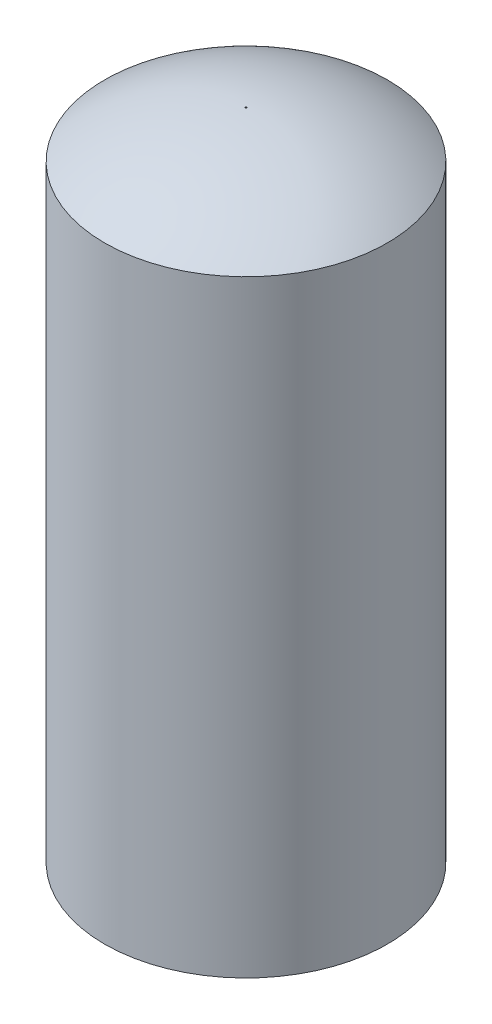
SolidWorks part; units mm, degrees
ref_plane "Спереди" through (0, 0, 0) normal (0, 0, 1) x (1, 0, 0)
ref_plane "Сверху" through (0, 0, 0) normal (0, 1, 0) x (1, 0, 0)
ref_plane "Справа" through (0, 0, 0) normal (1, 0, 0) x (0, 0, -1)
other "Центр тяжести" [suppressed]
sketch "Эскиз1" plane through (0, 0, 0) normal (1, 0, 0) x (0, 0, -1)
  line L0 (0, -42.7351) -> (0, 1057.9575) construction
  line L1 (200, 65.4384) -> (200, 934.5616)
  line L2 (-27.445, 500) -> (242.3332, 500) construction
  arc A0 (1, 1000) -> (200, 934.5616) centre (0.5, 663.1779) cw
  arc A1 (1, 0) -> (200, 65.4384) centre (0.5, 336.8221) ccw
  point P12 (200, 500)
  point P14 (0, 500)
revolve "Повернуть-Тонкостенный3" add sketch "Эскиз1" angle 360 about L0
surface "Поверхность-Заполнить3" [suppressed]
surface "Поверхность-Заполнить4" [suppressed]
surface "Поверхность-Сшить4" [suppressed]
